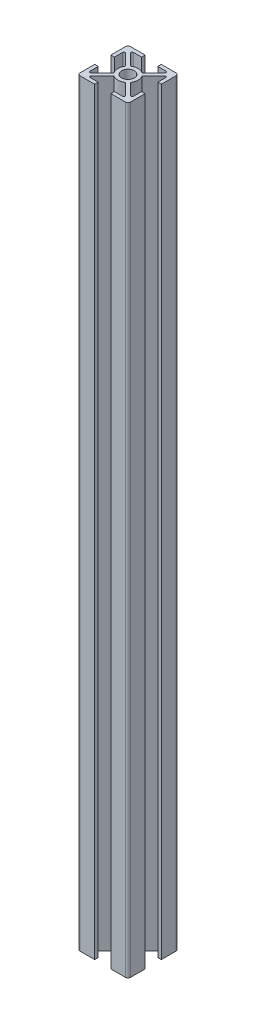
SolidWorks part; units mm, degrees
ref_plane "Front Plane" through (0, 0, 0) normal (0, 0, 1) x (1, 0, 0)
ref_plane "Top Plane" through (0, 0, 0) normal (0, 1, 0) x (1, 0, 0)
ref_plane "Right Plane" through (0, 0, 0) normal (1, 0, 0) x (0, 0, -1)
sketch "Sketch1" plane through (0, 0, 0) normal (0, 1, 0) x (1, 0, 0)
  line L0 (3.2, 10) -> (3.2, 8.6)
  line L1 (10, -3.2) -> (10, -10)
  line L2 (10, -3.2) -> (8.6, -3.2)
  line L3 (3.2, 10) -> (10, 10)
  line L4 (10, 3.2) -> (10, 10)
  line L5 (-10, -10) -> (10, 10) construction
  line L6 (-10, 10) -> (10, -10) construction
  line L7 (3.2, 8.6) -> (7.6101, 8.6)
  line L8 (7.6101, 8.6) -> (2.2898, 3.2798)
  line L9 (3.2798, 2.2898) -> (8.6, 7.6101)
  line L10 (8.6, 7.6101) -> (8.6, 3.2)
  line L11 (8.6, 3.2) -> (10, 3.2)
  line L12 (8.6, -3.2) -> (8.6, -7.6101)
  line L13 (8.6, -7.6101) -> (3.2798, -2.2898)
  line L14 (2.2898, -3.2798) -> (7.6101, -8.6)
  line L15 (7.6101, -8.6) -> (3.2, -8.6)
  line L16 (3.2, -10) -> (10, -10)
  line L17 (3.2, -8.6) -> (3.2, -10)
  line L18 (-3.2, -10) -> (-10, -10)
  line L19 (-3.2, -10) -> (-3.2, -8.6)
  line L20 (-3.2, -8.6) -> (-7.6101, -8.6)
  line L21 (-7.6101, -8.6) -> (-2.2898, -3.2798)
  line L22 (-3.2798, -2.2898) -> (-8.6, -7.6101)
  line L23 (-8.6, -7.6101) -> (-8.6, -3.2)
  line L24 (-10, -3.2) -> (-10, -10)
  line L25 (-8.6, -3.2) -> (-10, -3.2)
  line L26 (-10, 3.2) -> (-10, 10)
  line L27 (-10, 3.2) -> (-8.6, 3.2)
  line L28 (-8.6, 3.2) -> (-8.6, 7.6101)
  line L29 (-8.6, 7.6101) -> (-3.2798, 2.2898)
  line L30 (-2.2898, 3.2798) -> (-7.6101, 8.6)
  line L31 (-7.6101, 8.6) -> (-3.2, 8.6)
  line L32 (-3.2, 10) -> (-10, 10)
  line L33 (-3.2, 8.6) -> (-3.2, 10)
  circle A0 centre (0, 0) radius 2.5
  arc A1 (2.2898, 3.2798) -> (-2.2898, 3.2798) centre (0, 0) ccw
  arc A2 (-3.2798, 2.2898) -> (-3.2798, -2.2898) centre (0, 0) ccw
  arc A3 (-2.2898, -3.2798) -> (2.2898, -3.2798) centre (0, 0) ccw
  arc A4 (3.2798, -2.2898) -> (3.2798, 2.2898) centre (0, 0) ccw
  point P0 (0, 0)
  point P46 (0, 0)
  dimension "D3" = 5
  dimension "D4" = 8
  dimension "D1" = 20
  dimension "D2" = 20
  dimension "D5" = 6.8
  dimension "D6" = 6.8
  dimension "D7" = 1.4
  dimension "D8" = 0.7
  dimension "D9" = 1.4
  dimension "D10" = 4
extrude "Boss-Extrude1" add sketch "Sketch1" along normal blind 300
fillet "Fillet1" radius 0.5 8 edges at (7.6101, 150, -8.6) (8.6, 150, -7.6101) (8.6, 150, 7.6101) (7.6101, 150, 8.6) (-7.6101, 150, 8.6) (-8.6, 150, 7.6101) (-8.6, 150, -7.6101) (-7.6101, 150, -8.6)
fillet "Fillet2" radius 1 4 edges at (-10, 150, 10) (10, 150, 10) (10, 150, -10) (-10, 150, -10)
